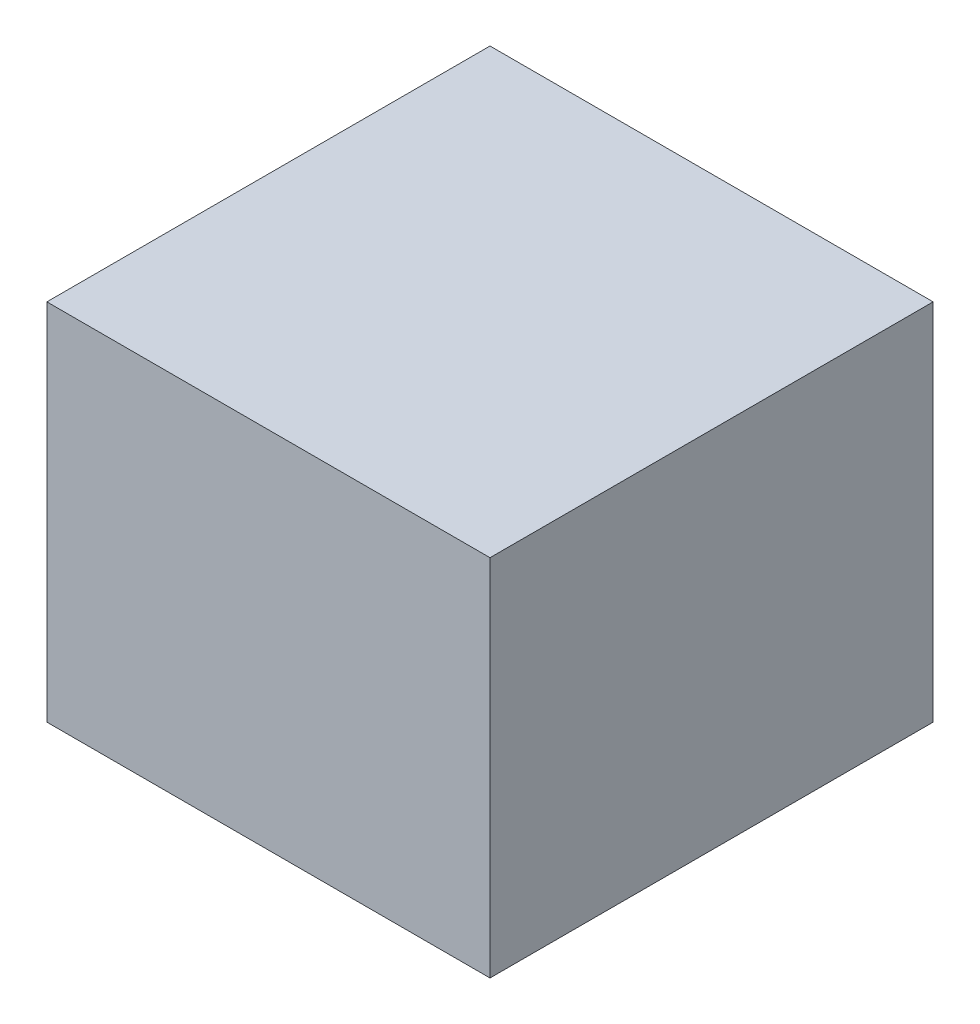
SolidWorks part; units mm, degrees
material "Beryllium S-200F, Vacuum Hot Pressed"
ref_plane "前视基准面" through (0, 0, 0) normal (0, 0, 1) x (1, 0, 0)
ref_plane "上视基准面" through (0, 0, 0) normal (0, 1, 0) x (1, 0, 0)
ref_plane "右视基准面" through (0, 0, 0) normal (1, 0, 0) x (0, 0, -1)
sketch "Sketch1" plane through (0, 0, 0) normal (0, 1, 0) x (1, 0, 0)
  line L1 (-70, 70) -> (70, 70)
  line L2 (-70, 70) -> (-70, -70)
  line L3 (-70, -70) -> (70, -70)
  line L4 (70, 70) -> (70, -70)
  line L5 (-70, 70) -> (70, -70) construction
  line L6 (-70, -70) -> (70, 70) construction
  point P0 (0, 0)
  dimension "D1" = 140
  dimension "D2" = 140
extrude "Boss-Extrude1" add sketch "Sketch1" along normal blind 115
